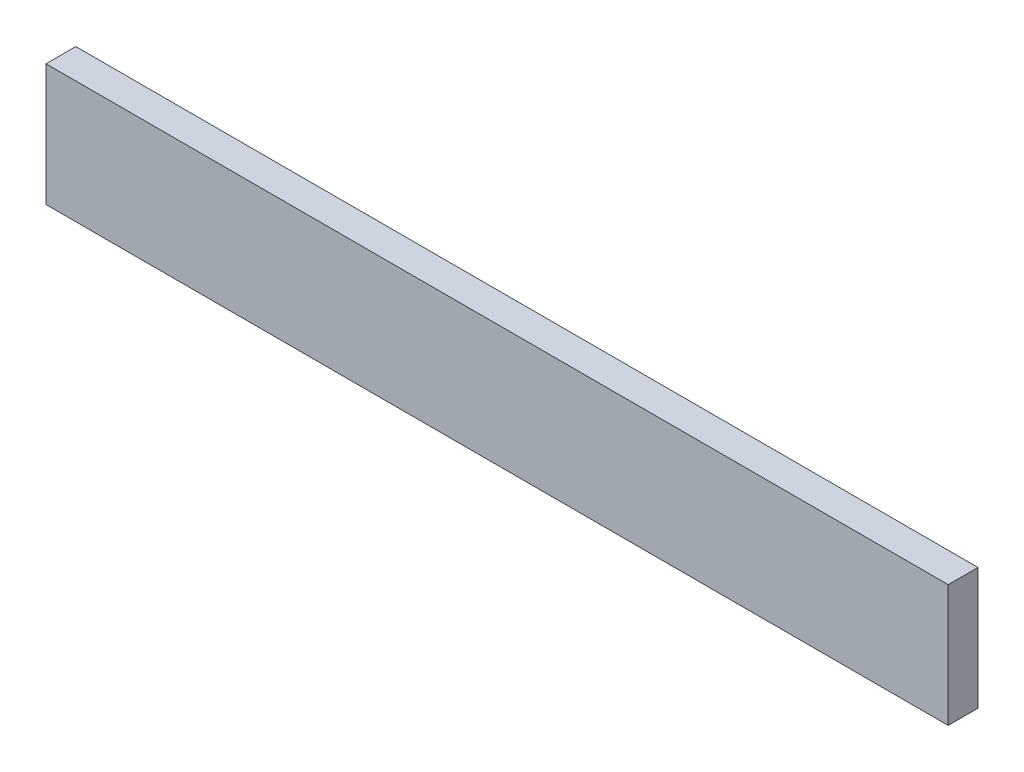
SolidWorks part; units mm, degrees
ref_plane "Face" through (0, 0, 0) normal (0, 0, 1) x (1, 0, 0)
ref_plane "Dessus" through (0, 0, 0) normal (0, 1, 0) x (1, 0, 0)
ref_plane "Droite" through (0, 0, 0) normal (1, 0, 0) x (0, 0, -1)
sketch "Esquisse1" plane through (0, 0, 0) normal (0, 0, 1) x (1, 0, 0)
  line L1 (0, 0) -> (666, 0)
  line L2 (0, 0) -> (0, 90)
  line L3 (0, 90) -> (666, 90)
  line L4 (666, 0) -> (666, 90)
  dimension "D1" = 666
  dimension "D2" = 90
extrude "Extrusion1" add sketch "Esquisse1" along normal blind 22
